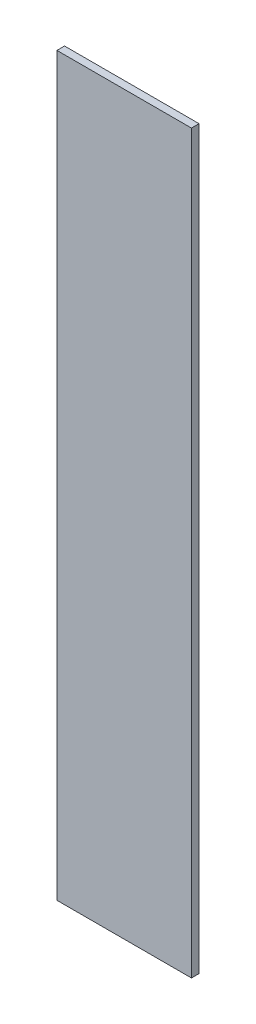
SolidWorks part; units mm, degrees
ref_plane "Plan de face" through (0, 0, 0) normal (0, 0, 1) x (1, 0, 0)
ref_plane "Plan de dessus" through (0, 0, 0) normal (0, 1, 0) x (1, 0, 0)
ref_plane "Plan de droite" through (0, 0, 0) normal (1, 0, 0) x (0, 0, -1)
sketch "Esquisse1" plane through (0, 0, 0) normal (0, 0, 1) x (1, 0, 0)
  line L1 (-60.6718, 31.2252) -> (-7.6718, 31.2252)
  line L2 (-60.6718, 31.2252) -> (-60.6718, -258.7748)
  line L3 (-60.6718, -258.7748) -> (-7.6718, -258.7748)
  line L4 (-7.6718, 31.2252) -> (-7.6718, -258.7748)
  dimension "D1" = 53
  dimension "D2" = 290
extrude "Boss.-Extru.1" add sketch "Esquisse1" along normal blind 3
equation "\"EpaisseurPlaque\"= 3"
equation "\"D1@Boss.-Extru.1\"=\"EpaisseurPlaque\""
equation "\"ProfondeurBoite\"=460"
equation "\"LongueurSyphon\"=170"
equation "\"LargeurSyphon\"=120"
equation "\"HauteurCoteDroit\"= 490"
equation "\"HauteurCoteGauche\"= 540"
equation "\"HauteurSolSyphon\"= 300"
equation "\"HauteurSyphon\"=\"HauteurCoteGauche\"-\"HauteurSolSyphon\""
equation "\"D2@Esquisse1\"= \"ProfondeurBoite\" - \"LongueurSyphon\""
equation "\"D1@Esquisse1\"= \"HauteurCoteGauche\" - \"HauteurCoteDroit\" + \"EpaisseurPlaque\""
equation "\"LargeurDroite\"=10"
equation "\"LargeurGauche\"=150"
equation "\"LargeurBoite\"= \"LargeurDroite\" + \"LargeurGauche\" + \"LargeurSyphon\""
